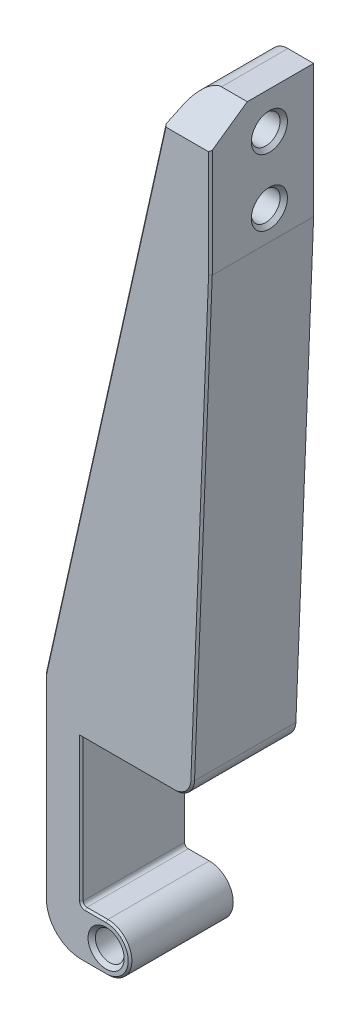
SolidWorks part; units mm, degrees
ref_plane "Front Plane" through (0, 0, 0) normal (0, 0, 1) x (1, 0, 0)
ref_plane "Top Plane" through (0, 0, 0) normal (0, 1, 0) x (1, 0, 0)
ref_plane "Right Plane" through (0, 0, 0) normal (1, 0, 0) x (0, 0, -1)
sketch "Sketch1" plane through (0, 0, 0) normal (0, 0, 1) x (1, 0, 0)
  line L0 (0, 0) -> (0, -38) construction
  line L1 (0, 0) -> (47, 0) construction
  line L2 (0, -38) -> (17.1313, -38) construction
  line L3 (6.7, -39.5) -> (1, -39.5)
  line L4 (0, -38.5) -> (0, 0)
  line L5 (0, 0) -> (25.1945, 0)
  line L6 (30.1905, 4.8017) -> (35, 126)
  line L7 (35, 126) -> (35, 162)
  line L8 (35, 162) -> (28.0051, 162)
  line L9 (-10, 9.4476) -> (-10, -42.5)
  line L10 (0, -52.5) -> (6.7, -52.5)
  line L11 (23.1257, 158.0914) -> (-9.8794, 10.5391)
  circle A0 centre (6.7, -46) radius 3.9
  arc A1 (6.7, -52.5) -> (6.7, -39.5) centre (6.7, -46) ccw
  arc A2 (-10, -42.5) -> (0, -52.5) centre (0, -42.5) ccw
  arc A3 (1, -39.5) -> (0, -38.5) centre (1, -38.5) cw
  arc A4 (25.1945, 0) -> (30.1905, 4.8017) centre (25.1945, 5) ccw
  arc A5 (-9.8794, 10.5391) -> (-10, 9.4476) centre (-5, 9.4476) ccw
  arc A6 (28.0051, 162) -> (23.1257, 158.0914) centre (28.0051, 157) ccw
  point P22 (30, 0)
  point P25 (-10, 10)
  point P28 (24, 162)
  dimension "D3" = 13
  dimension "D4" = 7.8
  dimension "D13" = 10
  dimension "D14" = 1
  dimension "D15" = 5
  dimension "D16" = 5
  dimension "D17" = 5
  dimension "D1" = 38
  dimension "D2" = 47
  dimension "D5" = 8
  dimension "D6" = 10
  dimension "D7" = 35
  dimension "D8" = 162
  dimension "D9" = 11
  dimension "D10" = 36
  dimension "D11" = 30
  dimension "D12" = 10
  dimension "D18" = 6.7
extrude "Boss-Extrude1" add sketch "Sketch1" along normal blind 28
sketch "Sketch4" plane through (35, 0, 0) normal (1, 0, 0) x (0, 0, -1)
  line L0 (-28, 162) -> (0, 162) construction
  line L1 (0, 126) -> (0, 162) construction
  circle A0 centre (-12, 152) radius 3.9
  circle A1 centre (-12, 134) radius 3.9
  dimension "D1" = 7.8
  dimension "D2" = 18
  dimension "D3" = 10
  dimension "D4" = 12
extrude "Cut-Extrude2" cut sketch "Sketch4" against normal blind 10
sketch "Sketch5" plane through (0, 0, 0) normal (0, 0, 1) x (1, 0, 0)
  line L0 (-4.4409, 16.528) -> (18.8775, 120.7752)
  line L2 (30.7281, 119.2276) -> (26.5811, 14.7224)
  line L3 (19.5866, 8) -> (2.3903, 8)
  line L6 (23.1257, 158.0914) -> (-9.8794, 10.5391) construction
  line L7 (30.1905, 4.8017) -> (35, 126) construction
  line L8 (0, 0) -> (25.1945, 0) construction
  arc A0 (30.7281, 119.2276) -> (18.8775, 120.7752) centre (24.7328, 119.4655) ccw
  arc A1 (26.5811, 14.7224) -> (19.5866, 8) centre (19.5866, 15) cw
  arc A2 (-4.4409, 16.528) -> (2.3903, 8) centre (2.3903, 15) ccw
  dimension "D3" = 6
  dimension "D4" = 7
  dimension "D1" = 4
  dimension "D2" = 4
  dimension "D5" = 8
extrude "Cut-Extrude3" cut sketch "Sketch5" along normal offset from surface (24 mm away) 4 up to face at (11.0339, 24.3637, 28)
chamfer "Chamfer1" distance 1 angle 45 4 edges at (10.6, -46, 0) (10.6, -46, 28) (35, 134, 8.1) (35, 152, 8.1)
sketch "Sketch6" plane through (35, 0, 0) normal (1, 0, 0) x (0, 0, -1)
  line L0 (-18, 162) -> (-28, 154.9979)
  line L1 (-28, 162) -> (0, 162) construction
  line L2 (-28, 126) -> (-28, 162) construction
  line L3 (-28, 154.9979) -> (-28, 162)
  line L4 (-28, 162) -> (-18, 162)
  dimension "D1" = 10
  dimension "D2" = 35
extrude "Cut-Extrude4" cut sketch "Sketch6" against normal through all
sketch "Sketch7" plane through (0, 0, 24) normal (0, 0, -1) x (-1, 0, 0)
  line L0 (-26.7219, 119.2563) -> (-22.4015, 78.1732)
  line L1 (-15.0221, 8) -> (-11, 8)
  line L2 (-11, 8) -> (-17.977, 74.3457)
  line L4 (-29.0884, 77.9079) -> (-28.9298, 73.911)
  line L5 (-26.5811, 14.7224) -> (-30.7281, 119.2276) construction
  line L6 (-28.9298, 73.911) -> (-21.9823, 74.1867)
  line L7 (-18.8775, 120.7752) -> (4.4409, 16.528) construction
  line L8 (-8.5754, 74.7187) -> (-9.463, 78.6867)
  line L9 (-18.8775, 120.7752) -> (4.4409, 16.528) construction
  line L10 (-9.463, 78.6867) -> (-18.3962, 78.3322)
  line L11 (-17.977, 74.3457) -> (-8.5754, 74.7187)
  line L12 (-21.9823, 74.1867) -> (-15.0221, 8)
  line L13 (-22.4015, 78.1732) -> (-29.0884, 77.9079)
  line L14 (-18.3962, 78.3322) -> (-22.7438, 119.6747)
  line L15 (-2.3903, 8) -> (-19.5866, 8) construction
  arc A0 (-18.8775, 120.7752) -> (-30.7281, 119.2276) centre (-24.7328, 119.4655) ccw construction
  arc A2 (-18.7657, 120.093) -> (-30.6999, 118.838) centre (-24.7328, 119.4655) ccw
  arc A3 (-26.7219, 119.2563) -> (-30.6999, 118.838) centre (-28.7109, 119.0472) ccw
  arc A4 (-18.7657, 120.093) -> (-22.7438, 119.6747) centre (-20.7548, 119.8838) ccw
  dimension "D3" = 2
  dimension "D7" = 4
  dimension "D1" = 4
  dimension "D2" = 4
  dimension "D4" = 11
  dimension "D5" = 75
extrude "Boss-Extrude2" add sketch "Sketch7" along normal blind 8
fillet "Fillet1" radius 3 10 edges at (15.0221, 8, 20) (11, 8, 20) (29.0884, 77.9079, 20) (28.9298, 73.911, 20) (17.977, 74.3457, 20) (21.9823, 74.1867, 20) (22.4015, 78.1732, 20) (18.3962, 78.3322, 20) (9.463, 78.6867, 20) (8.5754, 74.7187, 20)
chamfer "Chamfer2" distance 0.5 angle 45 13 edges at (6.2772, 82.7685, 28) (-9.9698, 9.9967, 28) (-10, -16.5262, 28) (-7.0711, -49.5711, 28) (3.35, -52.5, 28) (13.2, -46, 28) (3.85, -39.5, 28) (0.2929, -39.2071, 28) (0, -19.25, 28) (12.5972, 0, 28) (28.6592, 1.3951, 28) (32.5953, 65.4009, 28) (35, 140.499, 28)
